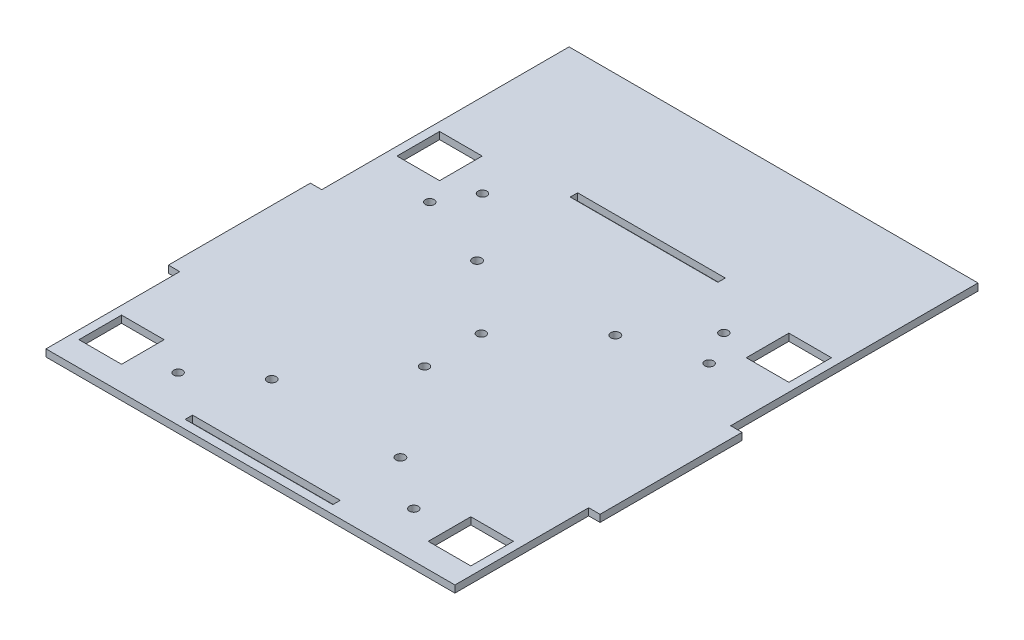
SolidWorks part; units mm, degrees
ref_plane "Front Plane" through (0, 0, 0) normal (0, 0, 1) x (1, 0, 0)
ref_plane "Top Plane" through (0, 0, 0) normal (0, 1, 0) x (1, 0, 0)
ref_plane "Right Plane" through (0, 0, 0) normal (1, 0, 0) x (0, 0, -1)
sketch "Sketch1" plane through (0, 0, 0) normal (0, 1, 0) x (1, 0, 0)
  line L5 (-72, -25) -> (-76, -25)
  line L7 (-72, 25) -> (-76, 25)
  line L21 (0, -78.079) -> (0, 78.079) construction
  line L22 (0, 0) -> (-74, 0) construction
  line L25 (72, -25) -> (76, -25)
  line L27 (72, 25) -> (76, 25)
  line L32 (69, 63.5) -> (54, 63.5)
  line L33 (-69, 48.5) -> (-54, 48.5)
  line L34 (-69, 48.5) -> (-69, 63.5)
  line L35 (-69, 63.5) -> (-54, 63.5)
  line L36 (-54, 48.5) -> (-54, 63.5)
  line L37 (54, 48.5) -> (54, 63.5)
  line L38 (69, 48.5) -> (54, 48.5)
  line L39 (69, 48.5) -> (69, 63.5)
  line L56 (-72, -72.1) -> (72, -72.1)
  line L57 (-26, -69.1) -> (26, -69.1)
  line L58 (-26, -69.1) -> (-26, -66.5)
  line L59 (-26, -66.5) -> (26, -66.5)
  line L60 (26, -69.1) -> (26, -66.5)
  line L63 (-26, 66.5) -> (26, 66.5)
  line L64 (26, 69.1) -> (26, 66.5)
  line L65 (-26, 69.1) -> (26, 69.1)
  line L66 (-26, 69.1) -> (-26, 66.5)
  line L67 (72, 25) -> (72, 72.1)
  line L68 (-72, 72.1) -> (72, 72.1)
  line L69 (-72, 25) -> (-72, 72.1)
  line L70 (-72, -25) -> (-72, -72.1)
  line L71 (72, -25) -> (72, -72.1)
  line L72 (-76, -25) -> (-76, 25)
  line L73 (76, -25) -> (76, 25)
  line L74 (69, -48.5) -> (54, -63.5) construction
  line L76 (-69, -63.5) -> (-54, -63.5)
  line L77 (-69, -63.5) -> (-69, -48.5)
  line L78 (-69, -48.5) -> (-54, -48.5)
  line L79 (-54, -63.5) -> (-54, -48.5)
  line L80 (-69, -63.5) -> (-54, -48.5) construction
  line L81 (-69, -48.5) -> (-54, -63.5) construction
  line L82 (69, -63.5) -> (54, -48.5) construction
  line L83 (69, -48.5) -> (54, -48.5)
  line L84 (54, -63.5) -> (54, -48.5)
  line L85 (69, -63.5) -> (54, -63.5)
  line L86 (69, -63.5) -> (69, -48.5)
  circle A4 centre (0, -10.8049) radius 1.55
  circle A5 centre (0, 9.1951) radius 1.55
  circle A6 centre (-49.1868, 40.2398) radius 1.55
  circle A7 centre (49.1868, 40.2398) radius 1.55
  circle A14 centre (-41.5002, -56.0811) radius 1.55
  circle A15 centre (41.5002, -56.0811) radius 1.55
  circle A16 centre (-23, 30.7017) radius 1.6
  circle A17 centre (24.1, 32.3017) radius 1.6
  circle A18 centre (23.5, -42.7983) radius 1.6
  circle A19 centre (-23, -41.5983) radius 1.6
  circle A20 centre (42.5, 52.1) radius 1.55
  circle A21 centre (-42.5, 52.1) radius 1.55
  point P0 (-61.5, -56)
  point P9 (0, 0)
  point P18 (0, -74)
  point P28 (-74, 0)
  point P97 (0, -67.8)
  dimension "D12" = 15
  dimension "D19" = 3
  dimension "D20" = 20
  dimension "D21" = 3
  dimension "D39" = 3.1
  dimension "D18" = 29.5
  dimension "D9" = 3.1
  dimension "D15" = 3.1
  dimension "D11" = 20
  dimension "D5" = 50
  dimension "D6" = 15
  dimension "D7" = 3
  dimension "D8" = 72.1
  dimension "D10" = 72
  dimension "D13" = 20
  dimension "D14" = 1.3
  dimension "D17" = 3
  dimension "D36" = 15
  dimension "D37" = 15
  dimension "D40" = 26
  dimension "D41" = 4
  dimension "D43" = 26
  dimension "D16" = 3
extrude "Boss-Extrude1" add sketch "Sketch1" along normal blind 2.5
sketch "Sketch2" plane through (0, 2.5, 0) normal (0, 1, 0) x (1, 0, 0)
  line L0 (-72, 72.1) -> (-72, 112.1)
  line L1 (-72, 112.1) -> (72, 112.1)
  line L2 (72, 112.1) -> (72, 72.1)
  line L12 (72, -25) -> (76, -25)
  line L13 (76, -25) -> (76, 25)
  line L14 (76, 25) -> (72, 25)
  line L15 (72, 25) -> (72, 72.1)
  line L16 (72, 72.1) -> (-72, 72.1)
  line L17 (-72, 72.1) -> (-72, 25)
  line L18 (-72, 25) -> (-76, 25)
  line L19 (-76, 25) -> (-76, -25)
  line L20 (-76, -25) -> (-72, -25)
  line L21 (-72, -25) -> (-72, -72.1)
  line L22 (-72, -72.1) -> (72, -72.1)
  line L23 (72, -72.1) -> (72, -25)
  line L24 (72, -25) -> (76, -25)
  line L25 (76, -25) -> (76, 25)
  line L26 (76, 25) -> (72, 25)
  line L27 (72, 25) -> (72, 72.1)
  line L28 (72, 72.1) -> (-72, 72.1)
  line L29 (-72, 72.1) -> (-72, 25)
  line L30 (-72, 25) -> (-76, 25)
  line L31 (-76, 25) -> (-76, -25)
  line L32 (-76, -25) -> (-72, -25)
  line L33 (-72, -25) -> (-72, -72.1)
  line L34 (-72, -72.1) -> (72, -72.1)
  line L35 (72, -72.1) -> (72, -25)
  line M51 (72, 72.1) -> (-72, 72.1)
  dimension "D2" = 40
  dimension "D1" = 0
extrude "Boss-Extrude2" add sketch "Sketch2" against normal blind 2.5 contours L2 L1 L0 M51
sketch "Sketch4" plane through (0, 2.5, 0) normal (0, 1, 0) x (1, 0, 0)
  line L0 (26, 69.1) -> (26, 66.5) construction
  line L1 (-26, 66.5) -> (26, 66.5) construction
  line L2 (-26, 69.1) -> (26, 69.1) construction
  line L3 (-26, 69.1) -> (-26, 66.5) construction
  line L4 (-54, 48.5) -> (-54, 63.5) construction
  line L5 (-69, 48.5) -> (-54, 48.5) construction
  line L6 (-69, 48.5) -> (-69, 63.5) construction
  line L7 (-69, 63.5) -> (-54, 63.5) construction
  line L8 (26, 69.1) -> (26, 66.5)
  line L9 (-26, 66.5) -> (26, 66.5)
  line L10 (-26, 69.1) -> (26, 69.1)
  line L11 (-26, 69.1) -> (-26, 66.5)
  line L12 (72, -25) -> (76, -25)
  line L13 (76, -25) -> (76, 25)
  line L14 (76, 25) -> (72, 25)
  line L15 (72, 25) -> (72, 112.1)
  line L16 (72, 112.1) -> (-72, 112.1)
  line L17 (-72, 112.1) -> (-72, 25)
  line L18 (-72, 25) -> (-76, 25)
  line L19 (-76, 25) -> (-76, -25)
  line L20 (-76, -25) -> (-72, -25)
  line L21 (-72, -25) -> (-72, -72.1)
  line L22 (-72, -72.1) -> (72, -72.1)
  line L23 (72, -72.1) -> (72, -25)
  line L24 (72, -25) -> (76, -25)
  line L25 (76, -25) -> (76, 25)
  line L26 (76, 25) -> (72, 25)
  line L27 (72, 25) -> (72, 112.1)
  line L28 (72, 112.1) -> (-72, 112.1)
  line L29 (-72, 112.1) -> (-72, 25)
  line L30 (-72, 25) -> (-76, 25)
  line L31 (-76, 25) -> (-76, -25)
  line L32 (-76, -25) -> (-72, -25)
  line L33 (-72, -25) -> (-72, -72.1)
  line L34 (-72, -72.1) -> (72, -72.1)
  line L35 (72, -72.1) -> (72, -25)
  line L36 (-54, 48.5) -> (-54, 63.5)
  line L37 (-69, 48.5) -> (-54, 48.5)
  line L38 (-69, 48.5) -> (-69, 63.5)
  line L39 (-69, 63.5) -> (-54, 63.5)
  line L46 (26, -69.1) -> (26, -66.5) construction
  line L47 (-26, -69.1) -> (26, -69.1) construction
  line L48 (-26, -69.1) -> (-26, -66.5) construction
  line L49 (-26, -66.5) -> (26, -66.5) construction
  line L50 (26, -69.1) -> (26, -66.5)
  line L51 (-26, -69.1) -> (26, -69.1)
  line L52 (-26, -69.1) -> (-26, -66.5)
  line L53 (-26, -66.5) -> (26, -66.5)
  line L54 (69, -63.5) -> (54, -63.5) construction
  line L55 (69, -63.5) -> (69, -48.5) construction
  line L56 (54, -63.5) -> (54, -48.5) construction
  line L57 (69, -48.5) -> (54, -48.5) construction
  line L58 (69, -63.5) -> (54, -63.5)
  line L59 (69, -63.5) -> (69, -48.5)
  line L60 (54, -63.5) -> (54, -48.5)
  line L61 (69, -48.5) -> (54, -48.5)
  line L62 (69, 48.5) -> (54, 48.5) construction
  line L63 (69, 48.5) -> (69, 63.5) construction
  line L64 (69, 63.5) -> (54, 63.5) construction
  line L65 (54, 48.5) -> (54, 63.5) construction
  line L66 (69, 48.5) -> (54, 48.5)
  line L67 (69, 48.5) -> (69, 63.5)
  line L68 (69, 63.5) -> (54, 63.5)
  line L69 (54, 48.5) -> (54, 63.5)
  line L70 (-54, -63.5) -> (-54, -48.5) construction
  line L71 (-69, -63.5) -> (-54, -63.5) construction
  line L72 (-69, -63.5) -> (-69, -48.5) construction
  line L73 (-69, -48.5) -> (-54, -48.5) construction
  line L74 (-54, -63.5) -> (-54, -48.5)
  line L75 (-69, -63.5) -> (-54, -63.5)
  line L76 (-69, -63.5) -> (-69, -48.5)
  line L77 (-69, -48.5) -> (-54, -48.5)
  circle A0 centre (-23, -41.5983) radius 1.6 construction
  circle A1 centre (0, -10.8049) radius 1.55 construction
  circle A2 centre (24.1, 32.3017) radius 1.6 construction
  circle A3 centre (0, 9.1951) radius 1.55 construction
  circle A4 centre (-23, 30.7017) radius 1.6 construction
  circle A5 centre (-49.1868, 40.2398) radius 1.55 construction
  circle A6 centre (-42.5, 52.1) radius 1.55 construction
  circle A7 centre (-23, -41.5983) radius 1.6
  circle A8 centre (0, -10.8049) radius 1.55
  circle A9 centre (24.1, 32.3017) radius 1.6
  circle A10 centre (0, 9.1951) radius 1.55
  circle A11 centre (-23, 30.7017) radius 1.6
  circle A12 centre (-49.1868, 40.2398) radius 1.55
  circle A13 centre (-42.5, 52.1) radius 1.55
  circle A15 centre (23.5, -42.7983) radius 1.6 construction
  circle A16 centre (41.5002, -56.0811) radius 1.55 construction
  circle A17 centre (41.5002, -56.0811) radius 1.55
  circle A18 centre (23.5, -42.7983) radius 1.6
  circle A19 centre (49.1868, 40.2398) radius 1.55 construction
  circle A20 centre (42.5, 52.1) radius 1.55 construction
  circle A21 centre (49.1868, 40.2398) radius 1.55
  circle A22 centre (42.5, 52.1) radius 1.55
  circle A23 centre (-41.5002, -56.0811) radius 1.55 construction
  circle A24 centre (-41.5002, -56.0811) radius 1.55
  dimension "D1" = 0
